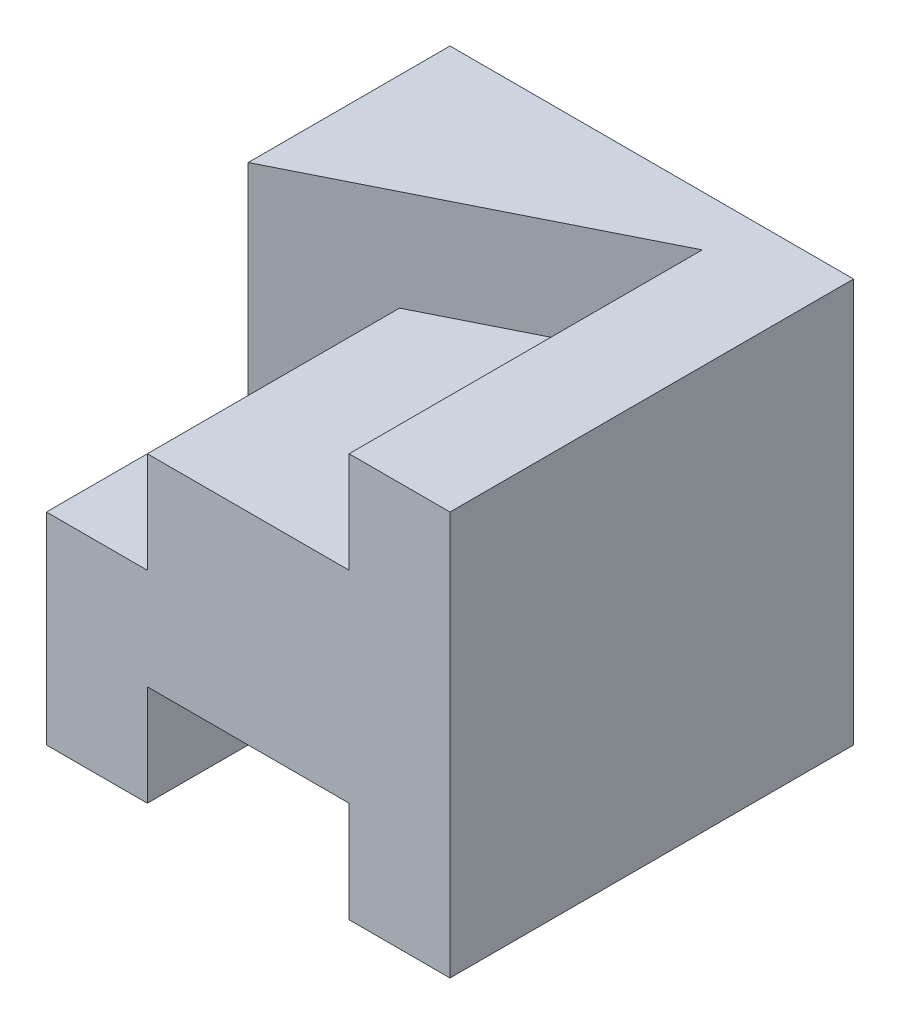
SolidWorks part; units mm, degrees
ref_plane "Front" through (0, 0, 0) normal (0, 0, 1) x (1, 0, 0)
ref_plane "Top" through (0, 0, 0) normal (0, 1, 0) x (1, 0, 0)
ref_plane "Right" through (0, 0, 0) normal (1, 0, 0) x (0, 0, -1)
sketch "Sketch1" plane through (0, 0, 0) normal (0, 0, 1) x (1, 0, 0)
  line L0 (0, 0) -> (0, 2)
  line L1 (0, 2) -> (1, 2)
  line L2 (1, 2) -> (1, 3)
  line L3 (1, 3) -> (3, 3)
  line L4 (3, 3) -> (3, 4)
  line L5 (3, 4) -> (4, 4)
  line L6 (4, 4) -> (4, 0)
  line L7 (4, 0) -> (3, 0)
  line L8 (3, 0) -> (3, 1)
  line L9 (3, 1) -> (1, 1)
  line L10 (1, 1) -> (1, 0)
  line L11 (1, 0) -> (0, 0)
  dimension "D1" = 4
  dimension "D2" = 1
  dimension "D3" = 1
  dimension "D4" = 1
  dimension "D5" = 1
  dimension "D6" = 2
  dimension "D7" = 1
  dimension "D8" = 1
  dimension "D9" = 2
extrude "Boss-Extrude1" add sketch "Sketch1" along normal blind 4
sketch "Sketch6" plane through (0, 4, 0) normal (0, 1, 0) x (1, 0, 0)
  line L0 (4, 0) -> (0, -2)
  line L1 (0, -4) -> (0, 0) construction
  line L2 (0, -2) -> (0, 0)
  line L3 (0, 0) -> (4, 0)
extrude "Boss-Extrude4" add sketch "Sketch6" against normal blind 2
